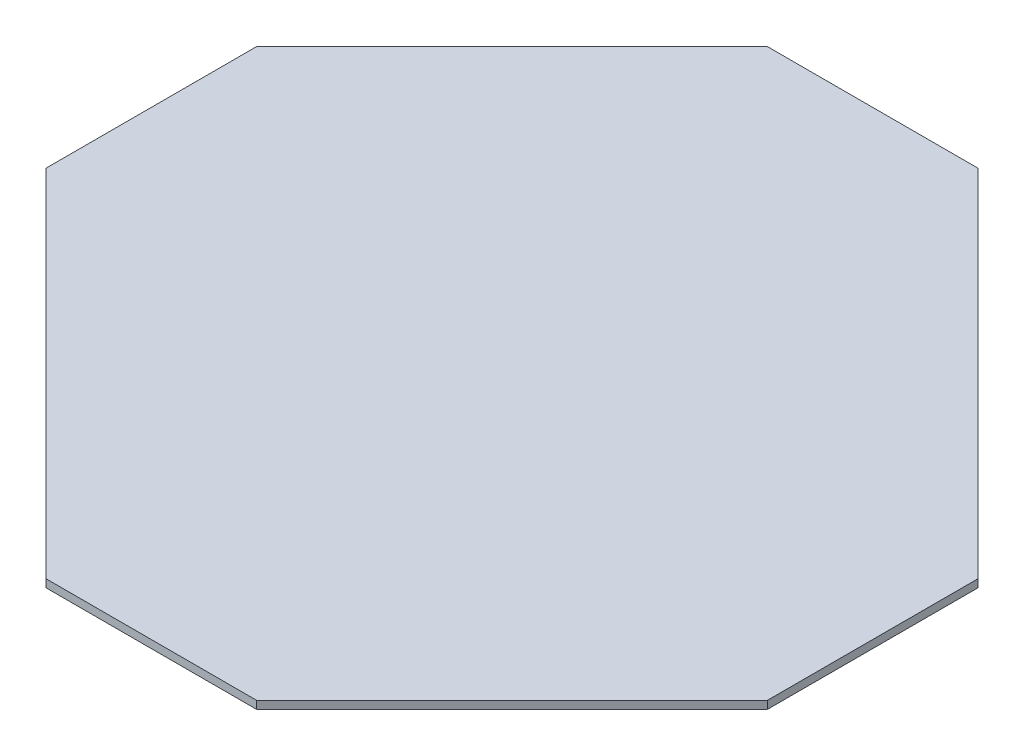
SolidWorks part; units mm, degrees
ref_plane "Front Plane" through (0, 0, 0) normal (0, 0, 1) x (1, 0, 0)
ref_plane "Top Plane" through (0, 0, 0) normal (0, 1, 0) x (1, 0, 0)
ref_plane "Right Plane" through (0, 0, 0) normal (1, 0, 0) x (0, 0, -1)
sketch "Sketch1" plane through (0, 0, 0) normal (0, 1, 0) x (1, 0, 0)
  line L0 (0, 0) -> (-88.7419, -88.7419) construction
  line L1 (68.75, -165.9772) -> (165.9772, -68.75) construction
  line L2 (165.9772, -68.75) -> (165.9772, 68.75) construction
  line L3 (165.9772, 68.75) -> (68.75, 165.9772) construction
  line L4 (68.75, 165.9772) -> (-68.75, 165.9772) construction
  line L5 (-68.75, 165.9772) -> (-165.9772, 68.75) construction
  line L6 (-165.9772, 68.75) -> (-165.9772, -68.75) construction
  line L7 (-165.9772, -68.75) -> (-68.75, -165.9772) construction
  line L8 (-68.75, -165.9772) -> (68.75, -165.9772) construction
  line L9 (117.3636, 117.3636) -> (-117.3636, -117.3636) construction
  line L10 (0, 0) -> (88.7419, 88.7419) construction
  line L11 (-88.7419, -88.7419) -> (-11.5066, -165.9772) construction
  line L12 (-11.5066, -165.9772) -> (-165.9772, -11.5066) construction
  line L13 (88.7419, 88.7419) -> (165.9772, 11.5066) construction
  line L14 (165.9772, 11.5066) -> (11.5066, 165.9772) construction
  circle A0 centre (0, 0) radius 165.9772 construction
  dimension "D1" = 137.5
sketch "Sketch3" plane through (0, 0, 0) normal (0, 1, 0) x (1, 0, 0)
  line L3 (146.9176, 30.5662) -> (11.5066, 165.9772)
  line L4 (11.5066, 165.9772) -> (-68.75, 165.9772)
  line L5 (-68.75, 165.9772) -> (-165.9772, 68.75)
  line L6 (-165.9772, 68.75) -> (-165.9772, -11.5066)
  line L7 (-165.9772, -11.5066) -> (-30.5662, -146.9176)
  line L8 (-68.75, 165.9772) -> (146.9176, -49.6904) construction
  line L9 (-165.9772, 68.75) -> (49.6904, -146.9176) construction
  line L10 (49.6904, -146.9176) -> (146.9176, -49.6904)
  line L11 (146.9176, 30.5662) -> (146.9176, -49.6904)
  line L12 (49.6904, -146.9176) -> (-30.5662, -146.9176)
  point P1 (165.9772, 11.5066)
  point P4 (0, 0)
  point P6 (-36.5115, -140.9723)
  point P19 (0, 0)
  point P21 (-11.5066, -165.9772)
  point P22 (0, 0)
extrude "Boss-Extrude2" add sketch "Sketch3" along normal blind 3
